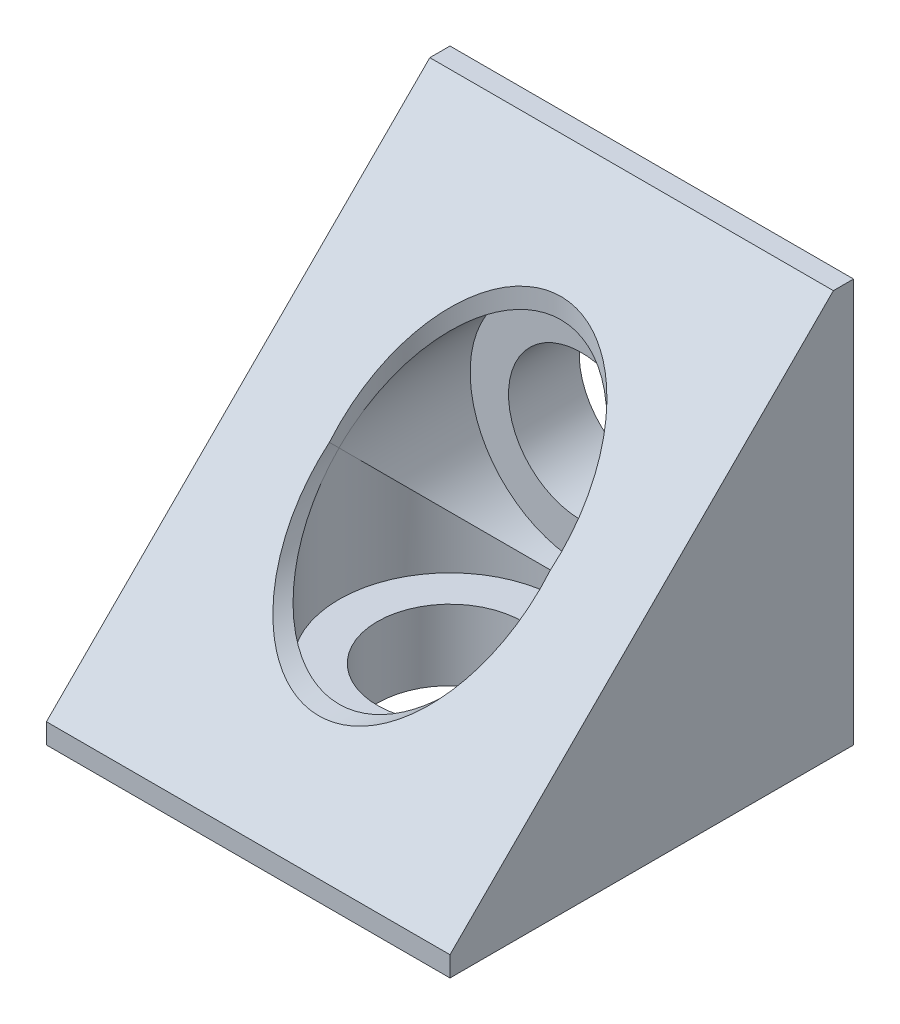
SolidWorks part; units mm, degrees
material "6061-T6 (SS)"
ref_plane "Front Plane" through (0, 0, 0) normal (0, 0, 1) x (1, 0, 0)
ref_plane "Top Plane" through (0, 0, 0) normal (0, 1, 0) x (1, 0, 0)
ref_plane "Right Plane" through (0, 0, 0) normal (1, 0, 0) x (0, 0, -1)
sketch "Sketch1" plane through (0, 0, 0) normal (0, 0, 1) x (1, 0, 0)
  line L1 (10, -10) -> (-10, -10)
  line L2 (10, -10) -> (10, 10)
  line L3 (10, 10) -> (-10, 10)
  line L4 (-10, -10) -> (-10, 10)
  line L5 (10, -10) -> (-10, 10) construction
  line L6 (10, 10) -> (-10, -10) construction
  circle A0 centre (0, 0) radius 3.6
  point P0 (0, 0)
  point P8 (0, 0)
  dimension "D2" = 7.2
  dimension "D1" = 20
extrude "Boss-Extrude1" add sketch "Sketch1" along normal mid plane 20
sketch "Sketch2" plane through (0, 0, 10) normal (0, 0, 1) x (1, 0, 0)
  circle A0 centre (0, 0) radius 5.5
  dimension "D1" = 11
extrude "Cut-Extrude1" cut sketch "Sketch2" against normal blind 16.5
sketch "Sketch4" plane through (0, 10, 0) normal (0, 1, 0) x (1, 0, 0)
  circle A0 centre (0, 0) radius 3.6
  dimension "D1" = 7.2
extrude "Cut-Extrude2" cut sketch "Sketch4" against normal through all
sketch "Sketch5" plane through (0, 10, 0) normal (0, 1, 0) x (1, 0, 0)
  circle A0 centre (0, 0) radius 5.5
  dimension "D1" = 11
extrude "Cut-Extrude3" cut sketch "Sketch5" against normal blind 16.5
sketch "Sketch6" plane through (10, 0, 0) normal (1, 0, 0) x (0, 0, -1)
  line L0 (-10, -9) -> (9, 10)
  line L1 (-10, -10) -> (-10, 10) construction
  line L2 (-10, 10) -> (10, 10) construction
  line L3 (9, 10) -> (-10, 10)
  line L4 (-10, 10) -> (-10, -9)
  line L5 (-10, -10) -> (10, -10) construction
  dimension "D1" = 1
  dimension "D2" = 45
extrude "Cut-Extrude4" cut sketch "Sketch6" against normal through all
